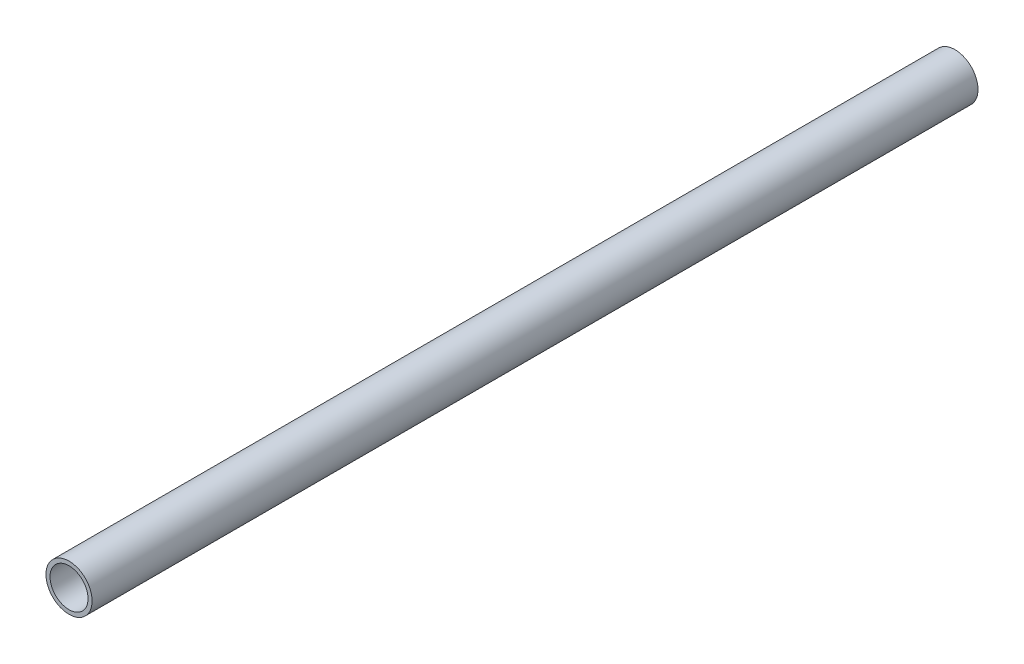
SolidWorks part; units mm, degrees
ref_plane "Front Plane" through (0, 0, 0) normal (0, 0, 1) x (1, 0, 0)
ref_plane "Top Plane" through (0, 0, 0) normal (0, 1, 0) x (1, 0, 0)
ref_plane "Right Plane" through (0, 0, 0) normal (1, 0, 0) x (0, 0, -1)
sketch "Sketch1" plane through (0, 0, 0) normal (0, 0, 1) x (1, 0, 0)
  circle A0 centre (0, 0) radius 15.875
  circle A1 centre (0, 0) radius 13.081
  dimension "D1" = 31.75
  dimension "D2" = 2.794
extrude "Boss-Extrude1" add sketch "Sketch1" along normal blind 609.6
